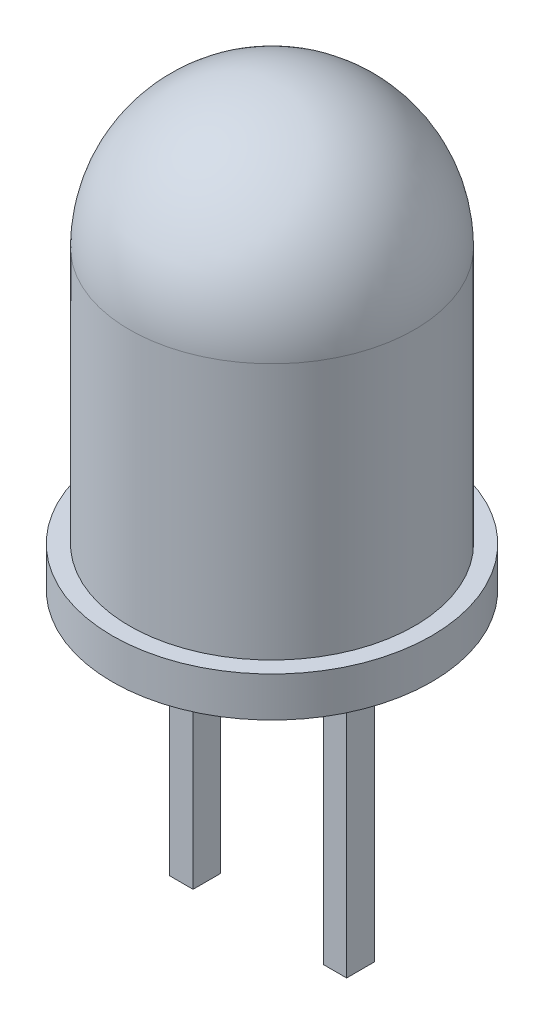
SolidWorks part; units mm, degrees
ref_plane "Front Plane" through (0, 0, 0) normal (0, 0, 1) x (1, 0, 0)
ref_plane "Top Plane" through (0, 0, 0) normal (0, 1, 0) x (1, 0, 0)
ref_plane "Right Plane" through (0, 0, 0) normal (1, 0, 0) x (0, 0, -1)
sketch "Sketch2" plane through (0, 0, 0) normal (0, 1, 0) x (1, 0, 0)
  circle A0 centre (0, 0) radius 2.5
  dimension "D1" = 5
extrude "Boss-Extrude1" add sketch "Sketch2" along normal blind 7
sketch "Sketch3" plane through (0, 0, 0) normal (0, -1, 0) x (1, 0, 0)
  circle A0 centre (0, 0) radius 2.8
extrude "Boss-Extrude2" add sketch "Sketch3" along normal blind 0.7
fillet "Fillet1" radius 2.5 1 edges at (0, 7, 2.5)
sketch "Sketch4" plane through (0, -0.7, 0) normal (0, -1, 0) x (1, 0, 0)
  line L0 (0, 1.6752) -> (0, -2.0522) construction
  line L1 (1.1419, -0.2424) -> (1.5513, -0.2424)
  line L2 (1.1419, -0.2424) -> (1.1419, 0.2424)
  line L3 (1.1419, 0.2424) -> (1.5513, 0.2424)
  line L4 (1.5513, -0.2424) -> (1.5513, 0.2424)
  line L5 (1.1419, -0.2424) -> (1.5513, 0.2424) construction
  line L6 (1.1419, 0.2424) -> (1.5513, -0.2424) construction
  line L7 (-1.1419, 0.2424) -> (-1.5513, -0.2424) construction
  line L8 (-1.1419, -0.2424) -> (-1.5513, 0.2424) construction
  line L9 (-1.5513, -0.2424) -> (-1.5513, 0.2424)
  line L10 (-1.1419, 0.2424) -> (-1.5513, 0.2424)
  line L11 (-1.1419, -0.2424) -> (-1.1419, 0.2424)
  line L12 (-1.1419, -0.2424) -> (-1.5513, -0.2424)
  point P0 (1.3466, 0)
  point P12 (-1.3466, 0)
extrude "Boss-Extrude3" add sketch "Sketch4" along normal blind 5
